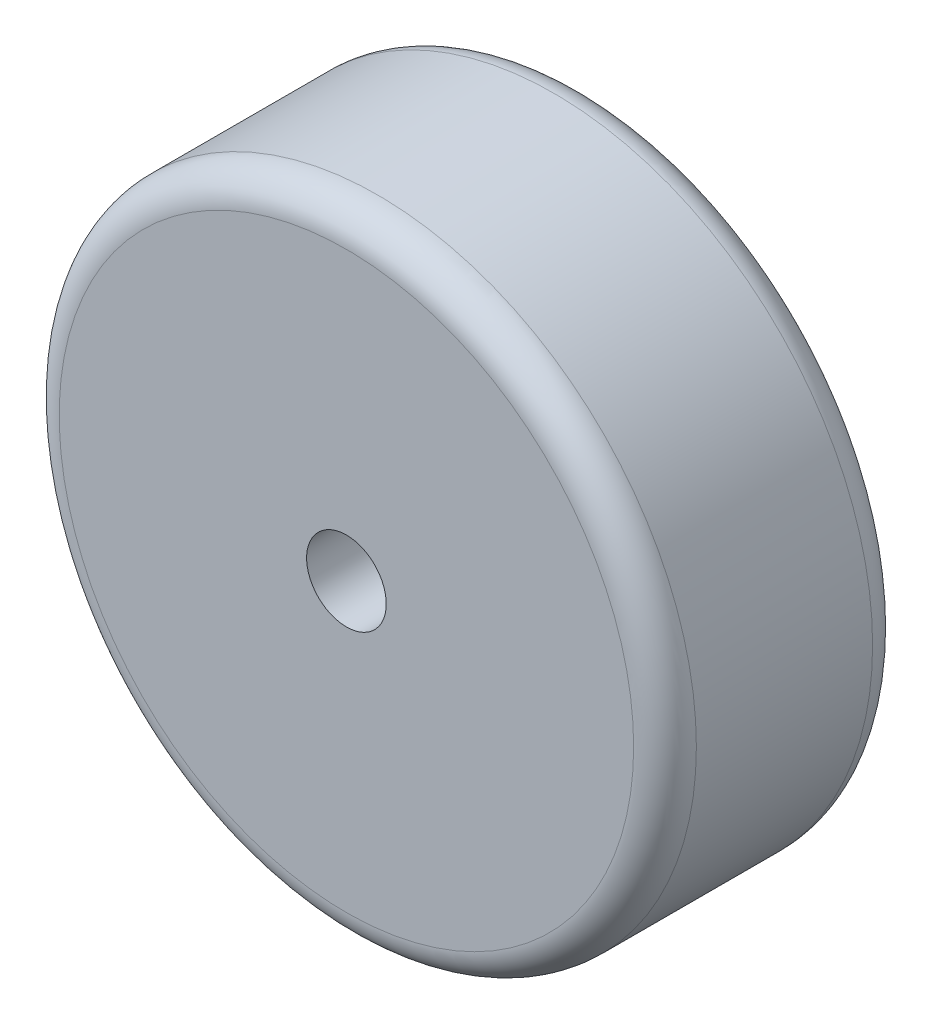
SolidWorks part; units mm, degrees
ref_plane "Front Plane" through (0, 0, 0) normal (0, 0, 1) x (1, 0, 0)
ref_plane "Top Plane" through (0, 0, 0) normal (0, 1, 0) x (1, 0, 0)
ref_plane "Right Plane" through (0, 0, 0) normal (1, 0, 0) x (0, 0, -1)
sketch "Sketch1" plane through (0, 0, 0) normal (0, 0, 1) x (1, 0, 0)
  circle A0 centre (0, 0) radius 101.6
  circle A1 centre (0, 0) radius 12.7
  dimension "D1" = 203.2
  dimension "D2" = 25.4
extrude "Boss-Extrude1" add sketch "Sketch1" along normal mid plane 76.2
fillet "Fillet1" radius 10 2 edges at (101.6, 0, 38.1) (101.6, 0, -38.1)
ref_plane "Plane1" through (0, 0, 0) normal (0, 0, 1) x (1, 0, 0)
